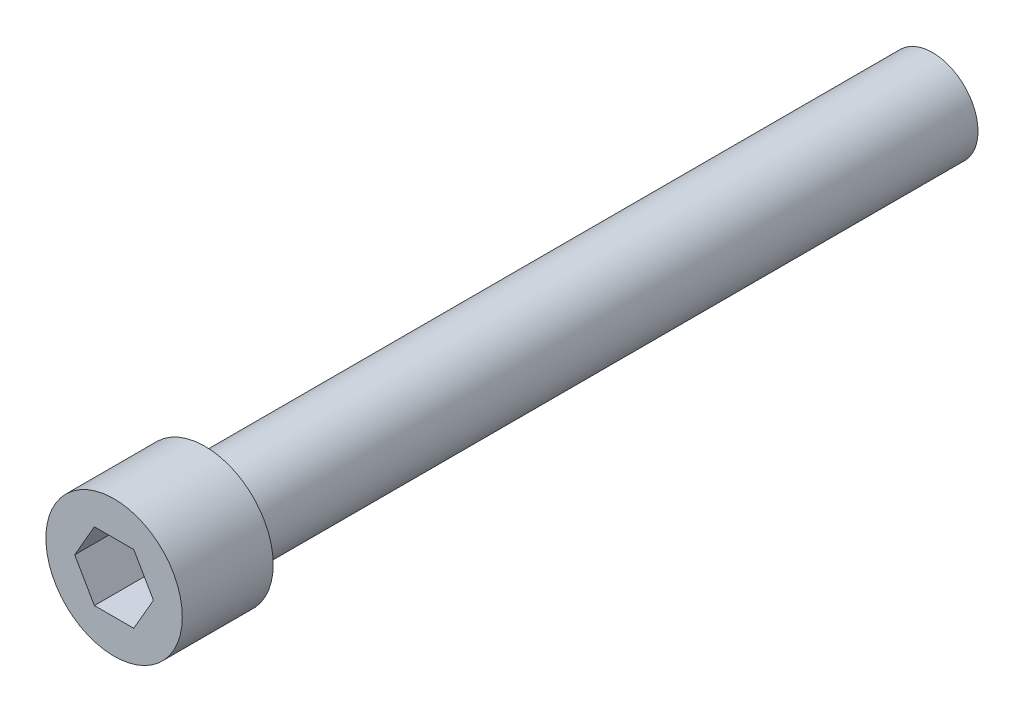
SolidWorks part; units mm, degrees
material "Alloy Steel"
ref_plane "Front Plane" through (0, 0, 0) normal (0, 0, 1) x (1, 0, 0)
ref_plane "Top Plane" through (0, 0, 0) normal (0, 1, 0) x (1, 0, 0)
ref_plane "Right Plane" through (0, 0, 0) normal (1, 0, 0) x (0, 0, -1)
sketch "Sketch1" plane through (0, 0, 0) normal (0, 0, 1) x (1, 0, 0)
  circle A0 centre (0, 0) radius 3.175
  dimension "D1" = 6.35
extrude "Boss-Extrude1" add sketch "Sketch1" along normal blind 50.8
sketch "Sketch2" plane through (0, 0, 50.8) normal (0, 0, 1) x (1, 0, 0)
  circle A0 centre (0, 0) radius 4.7625
  dimension "D1" = 9.525
extrude "Boss-Extrude2" add sketch "Sketch2" along normal blind 6.35
sketch "Sketch3" plane through (0, 0, 57.15) normal (0, 0, 1) x (1, 0, 0)
  line L1 (2.7496, 0) -> (1.3748, 2.3813)
  line L2 (1.3748, 2.3813) -> (-1.3748, 2.3813)
  line L3 (-1.3748, 2.3813) -> (-2.7496, 0)
  line L4 (-2.7496, 0) -> (-1.3748, -2.3813)
  line L5 (-1.3748, -2.3813) -> (1.3748, -2.3813)
  line L6 (1.3748, -2.3813) -> (2.7496, 0)
  circle A0 centre (0, 0) radius 2.3813 construction
  dimension "D1" = 4.7625
extrude "Cut-Extrude1" cut sketch "Sketch3" against normal blind 3.5814
